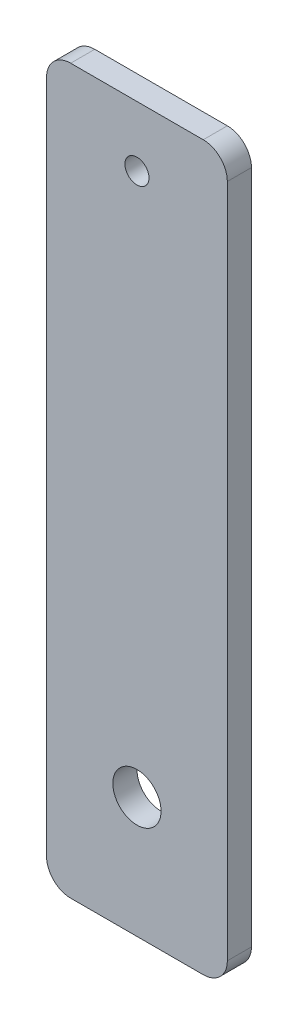
SolidWorks part; units mm, degrees
ref_plane "Ön Düzlem" through (0, 0, 0) normal (0, 0, 1) x (1, 0, 0)
ref_plane "Üst Düzlem" through (0, 0, 0) normal (0, 1, 0) x (1, 0, 0)
ref_plane "Sağ Düzlem" through (0, 0, 0) normal (1, 0, 0) x (0, 0, -1)
sketch "Sketch1" plane through (0, 0, 0) normal (0, 0, 1) x (1, 0, 0)
  line L1 (-7.5, 30) -> (7.5, 30)
  line L2 (-7.5, 30) -> (-7.5, -30)
  line L3 (-7.5, -30) -> (7.5, -30)
  line L4 (7.5, 30) -> (7.5, -30)
  line L5 (-7.5, 30) -> (7.5, -30) construction
  line L6 (-7.5, -30) -> (7.5, 30) construction
  circle A0 centre (0, -20) radius 2
  circle A1 centre (0, 25) radius 1
  point P0 (0, 0)
  point P10 (0, 0)
  point P12 (-1.138, 33.2694)
  dimension "D2" = 4
  dimension "D4" = 2
  dimension "D1" = 15
  dimension "D3" = 10
  dimension "D5" = 5
  dimension "D6" = 45
extrude "Boss-Extrude1" add sketch "Sketch1" along normal blind 2
fillet "Fillet1" radius 2 4 edges at (7.5, -30, 1) (-7.5, -30, 1) (-7.5, 30, 1) (7.5, 30, 1)
